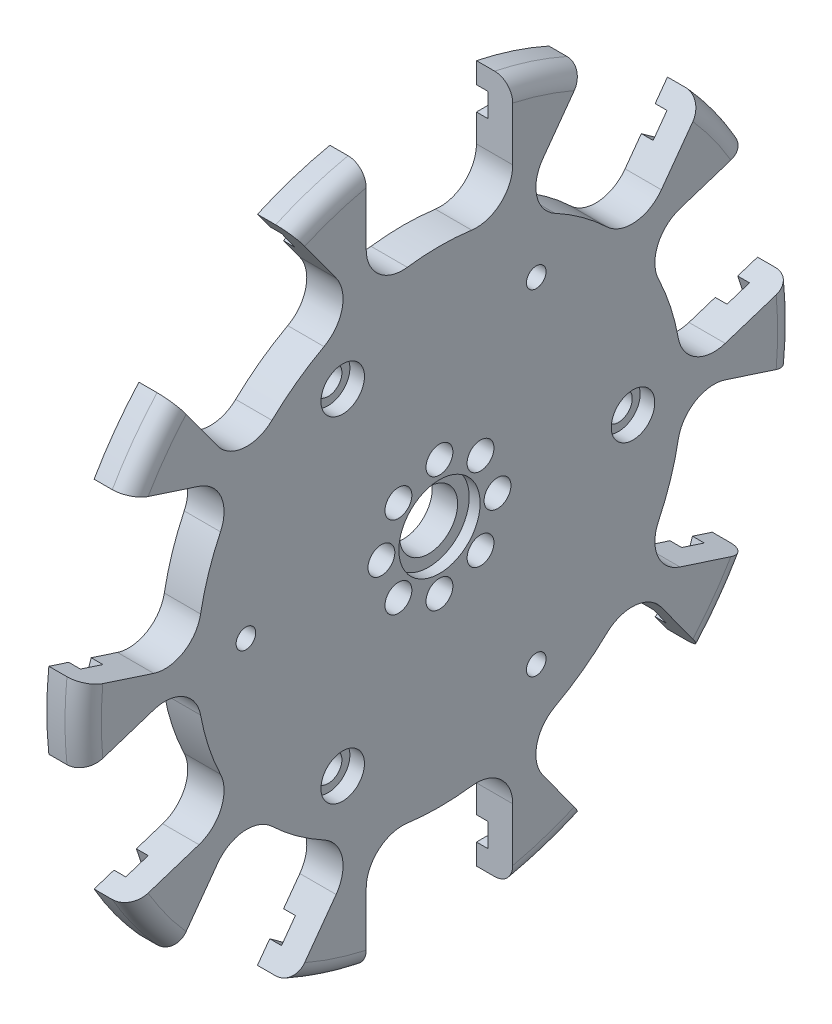
SolidWorks part; units mm, degrees
material "Delrin 2700 NC010, Low Viscosity Acetal Copolymer (SS)"
ref_plane "Front Plane" through (0, 0, 0) normal (0, 0, 1) x (1, 0, 0)
ref_plane "Top Plane" through (0, 0, 0) normal (0, 1, 0) x (1, 0, 0)
ref_plane "Right Plane" through (0, 0, 0) normal (1, 0, 0) x (0, 0, -1)
sketch "Sketch1" plane through (0, 0, 0) normal (1, 0, 0) x (0, 0, -1)
  line L0 (0, 0) -> (0, 8) construction
  line L1 (0, 8) -> (0, 49.1109) construction
  line L2 (10.0965, 48.0618) -> (10.0965, 38.1254)
  line L3 (-10.0965, 48.0618) -> (-10.0965, 38.1254)
  line L4 (20.0818, 44.8174) -> (14.2413, 36.7786)
  line L5 (36.4183, 32.9483) -> (30.5778, 24.9095)
  line L6 (42.5895, 24.4543) -> (33.1394, 21.3837)
  line L7 (48.8295, 5.2496) -> (39.3794, 2.179)
  line L8 (48.8295, -5.2496) -> (39.3794, -2.179)
  line L9 (42.5895, -24.4543) -> (33.1394, -21.3837)
  line L10 (36.4183, -32.9483) -> (30.5778, -24.9095)
  line L11 (20.0818, -44.8174) -> (14.2413, -36.7786)
  line L12 (10.0965, -48.0618) -> (10.0965, -38.1254)
  line L13 (-10.0965, -48.0618) -> (-10.0965, -38.1254)
  line L14 (-20.0818, -44.8174) -> (-14.2413, -36.7786)
  line L15 (-36.4183, -32.9483) -> (-30.5778, -24.9095)
  line L16 (-42.5895, -24.4543) -> (-33.1394, -21.3837)
  line L17 (-48.8295, -5.2496) -> (-39.3794, -2.179)
  line L18 (-48.8295, 5.2496) -> (-39.3794, 2.179)
  line L19 (-42.5895, 24.4543) -> (-33.1394, 21.3837)
  line L20 (-36.4183, 32.9483) -> (-30.5778, 24.9095)
  line L21 (-20.0818, 44.8174) -> (-14.2413, 36.7786)
  line L22 (-26.67, 0) -> (26.67, 0) construction
  arc A0 (-10.0965, 48.0618) -> (-20.0818, 44.8174) centre (0, 0) ccw
  arc A1 (4.434, 33.1694) -> (-4.434, 33.1694) centre (0, 0) ccw
  circle A2 centre (0, 0) radius 4
  circle A3 centre (0, 8) radius 1.85
  arc A4 (-10.0965, 38.1254) -> (-4.434, 33.1694) centre (-5.0965, 38.1254) ccw
  arc A5 (10.0965, 38.1254) -> (4.434, 33.1694) centre (5.0965, 38.1254) cw
  arc A6 (14.2413, 36.7786) -> (15.9093, 29.4409) centre (18.2864, 33.8397) ccw
  arc A7 (23.0837, 24.2284) -> (15.9093, 29.4409) centre (0, 0) ccw
  arc A8 (30.5778, 24.9095) -> (23.0837, 24.2284) centre (26.5327, 27.8484) cw
  arc A9 (33.1394, 21.3837) -> (30.1758, 14.4669) centre (34.6845, 16.6284) ccw
  arc A10 (32.9162, 6.0329) -> (30.1758, 14.4669) centre (0, 0) ccw
  arc A11 (39.3794, 2.179) -> (32.9162, 6.0329) centre (37.8343, 6.9343) cw
  arc A12 (39.3794, -2.179) -> (32.9162, -6.0329) centre (37.8343, -6.9343) ccw
  arc A13 (30.1758, -14.4669) -> (32.9162, -6.0329) centre (0, 0) ccw
  arc A14 (33.1394, -21.3837) -> (30.1758, -14.4669) centre (34.6845, -16.6284) cw
  arc A15 (30.5778, -24.9095) -> (23.0837, -24.2284) centre (26.5327, -27.8484) ccw
  arc A16 (15.9093, -29.4409) -> (23.0837, -24.2284) centre (0, 0) ccw
  arc A17 (14.2413, -36.7786) -> (15.9093, -29.4409) centre (18.2864, -33.8397) cw
  arc A18 (10.0965, -38.1254) -> (4.434, -33.1694) centre (5.0965, -38.1254) ccw
  arc A19 (-4.434, -33.1694) -> (4.434, -33.1694) centre (0, 0) ccw
  arc A20 (-10.0965, -38.1254) -> (-4.434, -33.1694) centre (-5.0965, -38.1254) cw
  arc A21 (-14.2413, -36.7786) -> (-15.9093, -29.4409) centre (-18.2864, -33.8397) ccw
  arc A22 (-23.0837, -24.2284) -> (-15.9093, -29.4409) centre (0, 0) ccw
  arc A23 (-30.5778, -24.9095) -> (-23.0837, -24.2284) centre (-26.5327, -27.8484) cw
  arc A24 (-33.1394, -21.3837) -> (-30.1758, -14.4669) centre (-34.6845, -16.6284) ccw
  arc A25 (-32.9162, -6.0329) -> (-30.1758, -14.4669) centre (0, 0) ccw
  arc A26 (-39.3794, -2.179) -> (-32.9162, -6.0329) centre (-37.8343, -6.9343) cw
  arc A27 (-39.3794, 2.179) -> (-32.9162, 6.0329) centre (-37.8343, 6.9343) ccw
  arc A28 (-30.1758, 14.4669) -> (-32.9162, 6.0329) centre (0, 0) ccw
  arc A29 (-33.1394, 21.3837) -> (-30.1758, 14.4669) centre (-34.6845, 16.6284) cw
  arc A30 (-30.5778, 24.9095) -> (-23.0837, 24.2284) centre (-26.5327, 27.8484) ccw
  arc A31 (-15.9093, 29.4409) -> (-23.0837, 24.2284) centre (0, 0) ccw
  arc A32 (-14.2413, 36.7786) -> (-15.9093, 29.4409) centre (-18.2864, 33.8397) cw
  arc A33 (20.0818, 44.8174) -> (10.0965, 48.0618) centre (0, 0) ccw
  arc A34 (42.5895, 24.4543) -> (36.4183, 32.9483) centre (0, 0) ccw
  arc A35 (48.8295, -5.2496) -> (48.8295, 5.2496) centre (0, 0) ccw
  arc A36 (36.4183, -32.9483) -> (42.5895, -24.4543) centre (0, 0) ccw
  arc A37 (10.0965, -48.0618) -> (20.0818, -44.8174) centre (0, 0) ccw
  arc A38 (-20.0818, -44.8174) -> (-10.0965, -48.0618) centre (0, 0) ccw
  arc A39 (-42.5895, -24.4543) -> (-36.4183, -32.9483) centre (0, 0) ccw
  arc A40 (-48.8295, 5.2496) -> (-48.8295, -5.2496) centre (0, 0) ccw
  arc A41 (-36.4183, 32.9483) -> (-42.5895, 24.4543) centre (0, 0) ccw
  circle A42 centre (5.6569, 5.6569) radius 1.85
  circle A43 centre (8, 0) radius 1.85
  circle A44 centre (5.6569, -5.6569) radius 1.85
  circle A45 centre (0, -8) radius 1.85
  circle A46 centre (-5.6569, -5.6569) radius 1.85
  circle A47 centre (-8, 0) radius 1.85
  circle A48 centre (-5.6569, 5.6569) radius 1.85
  circle A49 centre (26.67, 0) radius 1.8987
  circle A50 centre (-26.67, 0) radius 1.3526
  circle A51 centre (-13.335, -23.0969) radius 1.8986
  circle A52 centre (13.335, 23.0969) radius 1.3525
  circle A53 centre (-13.335, 23.0969) radius 1.8987
  circle A54 centre (13.335, -23.0969) radius 1.3526
  point P13 (-10.0965, 31.9051)
  point P16 (10.0965, 31.9051)
  point P91 (0, 0)
  point P105 (0, 0)
  point P106 (0, 0)
  point P119 (0, 0)
  dimension "D1" = 98.2218
  dimension "D2" = 66.929
  dimension "D3" = 8
  dimension "D5" = 3.7
  dimension "D7" = 5
  dimension "D11" = 2.7051
  dimension "D12" = 3.7973
  dimension "D4" = 8
  dimension "D6" = 10.0965
  dimension "D10" = 53.34
  dimension "D8" = 10
  dimension "D9" = 8
  dimension "D13" = 3
extrude "Boss-Extrude1" add sketch "Sketch1" along normal blind 5
fillet "Fillet1" radius 2.5 10 edges at (5, 28.8667, 39.7316) (5, 0, 49.1109) (5, -28.8667, 39.7316) (5, -46.7072, 15.1761) (5, -46.7072, -15.1761) (5, -28.8667, -39.7316) (5, 0, -49.1109) (5, 28.8667, -39.7316) (5, 46.7072, -15.1761) (5, 46.7072, 15.1761)
sketch "Sketch2" plane through (0, 0, 0) normal (-1, 0, 0) x (0, 0, 1)
  line L0 (0, 0) -> (0, 43.561) construction
  line L1 (-12.8651, 43.561) -> (12.8651, 43.561) construction
  line L2 (-12.8651, 41.9354) -> (-12.8651, 45.1866)
  line L3 (-12.8651, 45.1866) -> (-10.0965, 45.1866)
  line L4 (-10.0965, 48.0618) -> (-10.0965, 38.1254) construction
  line L5 (-10.0965, 45.1866) -> (-10.0965, 41.9354)
  line L6 (-12.8651, 41.9354) -> (-10.0965, 41.9354)
  line L7 (12.8651, 41.9354) -> (10.0965, 41.9354)
  line L8 (10.0965, 45.1866) -> (10.0965, 41.9354)
  line L9 (12.8651, 45.1866) -> (10.0965, 45.1866)
  line L10 (12.8651, 41.9354) -> (12.8651, 45.1866)
  line L11 (16.1519, 44.1186) -> (18.3918, 42.4913)
  line L12 (14.2409, 41.4884) -> (16.1519, 44.1186)
  line L13 (14.2409, 41.4884) -> (16.4808, 39.861)
  line L14 (18.3918, 42.4913) -> (16.4808, 39.861)
  line L15 (34.7283, 30.6222) -> (32.8172, 27.9919)
  line L16 (36.9681, 28.9948) -> (34.7283, 30.6222)
  line L17 (35.0571, 26.3645) -> (36.9681, 28.9948)
  line L18 (35.0571, 26.3645) -> (32.8172, 27.9919)
  line L19 (38.9995, 26.1989) -> (39.855, 23.5658)
  line L20 (35.9074, 25.1942) -> (38.9995, 26.1989)
  line L21 (35.9074, 25.1942) -> (36.7629, 22.5611)
  line L22 (39.855, 23.5658) -> (36.7629, 22.5611)
  line L23 (46.095, 4.3611) -> (43.0029, 3.3564)
  line L24 (46.9505, 1.728) -> (46.095, 4.3611)
  line L25 (43.8585, 0.7233) -> (46.9505, 1.728)
  line L26 (43.8585, 0.7233) -> (43.0029, 3.3564)
  line L27 (46.9505, -1.728) -> (46.095, -4.3611)
  line L28 (43.8585, -0.7233) -> (46.9505, -1.728)
  line L29 (43.8585, -0.7233) -> (43.0029, -3.3564)
  line L30 (46.095, -4.3611) -> (43.0029, -3.3564)
  line L31 (39.855, -23.5658) -> (36.7629, -22.5611)
  line L32 (38.9995, -26.1989) -> (39.855, -23.5658)
  line L33 (35.9074, -25.1942) -> (38.9995, -26.1989)
  line L34 (35.9074, -25.1942) -> (36.7629, -22.5611)
  line L35 (36.9681, -28.9948) -> (34.7283, -30.6222)
  line L36 (35.0571, -26.3645) -> (36.9681, -28.9948)
  line L37 (35.0571, -26.3645) -> (32.8172, -27.9919)
  line L38 (34.7283, -30.6222) -> (32.8172, -27.9919)
  line L39 (18.3918, -42.4913) -> (16.4808, -39.861)
  line L40 (16.1519, -44.1186) -> (18.3918, -42.4913)
  line L41 (14.2409, -41.4884) -> (16.1519, -44.1186)
  line L42 (14.2409, -41.4884) -> (16.4808, -39.861)
  line L43 (12.8651, -45.1866) -> (10.0965, -45.1866)
  line L44 (12.8651, -41.9354) -> (12.8651, -45.1866)
  line L45 (12.8651, -41.9354) -> (10.0965, -41.9354)
  line L46 (10.0965, -45.1866) -> (10.0965, -41.9354)
  line L47 (-10.0965, -45.1866) -> (-10.0965, -41.9354)
  line L48 (-12.8651, -45.1866) -> (-10.0965, -45.1866)
  line L49 (-12.8651, -41.9354) -> (-12.8651, -45.1866)
  line L50 (-12.8651, -41.9354) -> (-10.0965, -41.9354)
  line L51 (-16.1519, -44.1186) -> (-18.3918, -42.4913)
  line L52 (-14.2409, -41.4884) -> (-16.1519, -44.1186)
  line L53 (-14.2409, -41.4884) -> (-16.4808, -39.861)
  line L54 (-18.3918, -42.4913) -> (-16.4808, -39.861)
  line L55 (-34.7283, -30.6222) -> (-32.8172, -27.9919)
  line L56 (-36.9681, -28.9948) -> (-34.7283, -30.6222)
  line L57 (-35.0571, -26.3645) -> (-36.9681, -28.9948)
  line L58 (-35.0571, -26.3645) -> (-32.8172, -27.9919)
  line L59 (-38.9995, -26.1989) -> (-39.855, -23.5658)
  line L60 (-35.9074, -25.1942) -> (-38.9995, -26.1989)
  line L61 (-35.9074, -25.1942) -> (-36.7629, -22.5611)
  line L62 (-39.855, -23.5658) -> (-36.7629, -22.5611)
  line L63 (-46.095, -4.3611) -> (-43.0029, -3.3564)
  line L64 (-46.9505, -1.728) -> (-46.095, -4.3611)
  line L65 (-43.8585, -0.7233) -> (-46.9505, -1.728)
  line L66 (-43.8585, -0.7233) -> (-43.0029, -3.3564)
  line L67 (-46.9505, 1.728) -> (-46.095, 4.3611)
  line L68 (-43.8585, 0.7233) -> (-46.9505, 1.728)
  line L69 (-43.8585, 0.7233) -> (-43.0029, 3.3564)
  line L70 (-46.095, 4.3611) -> (-43.0029, 3.3564)
  line L71 (-39.855, 23.5658) -> (-36.7629, 22.5611)
  line L72 (-38.9995, 26.1989) -> (-39.855, 23.5658)
  line L73 (-35.9074, 25.1942) -> (-38.9995, 26.1989)
  line L74 (-35.9074, 25.1942) -> (-36.7629, 22.5611)
  line L75 (-36.9681, 28.9948) -> (-34.7283, 30.6222)
  line L76 (-35.0571, 26.3645) -> (-36.9681, 28.9948)
  line L77 (-35.0571, 26.3645) -> (-32.8172, 27.9919)
  line L78 (-34.7283, 30.6222) -> (-32.8172, 27.9919)
  line L79 (-18.3918, 42.4913) -> (-16.4808, 39.861)
  line L80 (-16.1519, 44.1186) -> (-18.3918, 42.4913)
  line L81 (-14.2409, 41.4884) -> (-16.1519, 44.1186)
  line L82 (-14.2409, 41.4884) -> (-16.4808, 39.861)
  point P5 (0, 43.561)
  point P12 (-10.0965, 43.561)
  point P91 (0, 0)
  dimension "D1" = 43.561
  dimension "D2" = 25.7302
  dimension "D3" = 1.6256
  dimension "D4" = 10
extrude "Cut-Extrude1" cut sketch "Sketch2" against normal blind 1.6256
sketch "Sketch3" plane through (5, 0, 0) normal (1, 0, 0) x (0, 0, -1)
  circle A0 centre (26.67, 0) radius 2.9972
  circle A1 centre (-13.335, -23.0969) radius 2.9972
  circle A2 centre (-13.335, 23.0969) radius 2.9972
  point P9 (0, 0)
  dimension "D1" = 5.9944
  dimension "D2" = 3
extrude "Cut-Extrude2" cut sketch "Sketch3" against normal blind 2.0066
sketch "Sketch4" plane through (5, 0, 0) normal (1, 0, 0) x (0, 0, -1)
  circle A0 centre (0, 0) radius 5.6007
  dimension "D1" = 11.2014
extrude "Cut-Extrude3" cut sketch "Sketch4" against normal blind 1.4986
